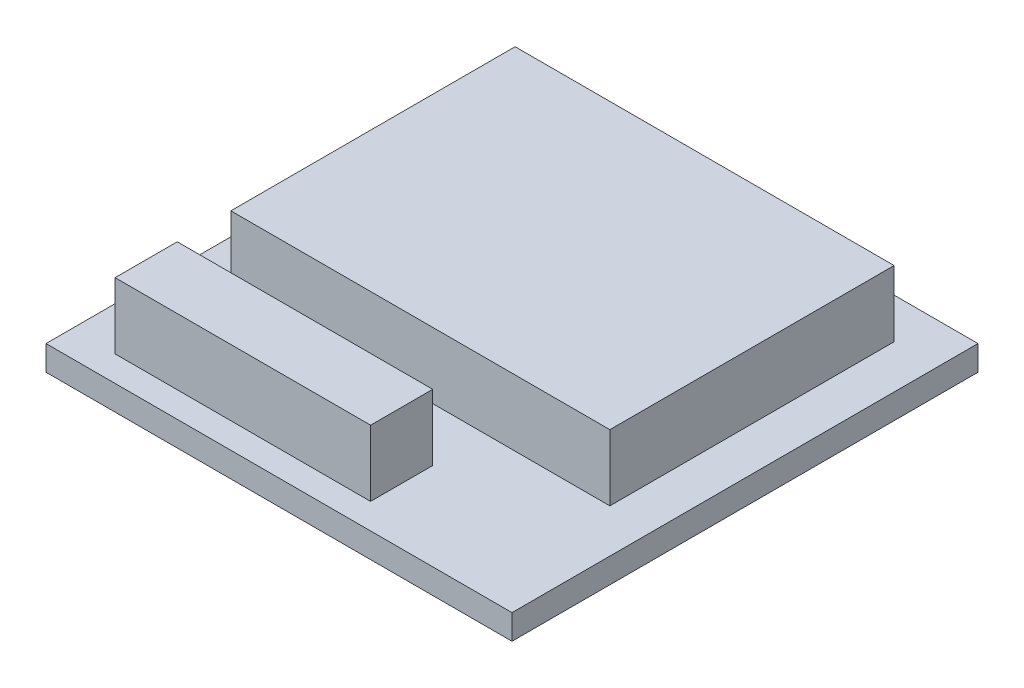
SolidWorks part; units mm, degrees
ref_plane "Front Plane" through (0, 0, 0) normal (0, 0, 1) x (1, 0, 0)
ref_plane "Top Plane" through (0, 0, 0) normal (0, 1, 0) x (1, 0, 0)
ref_plane "Right Plane" through (0, 0, 0) normal (1, 0, 0) x (0, 0, -1)
sketch "Sketch1" plane through (0, 0, 0) normal (0, 1, 0) x (1, 0, 0)
  line L1 (-7.62, -7.62) -> (7.62, -7.62)
  line L2 (-7.62, -7.62) -> (-7.62, 7.62)
  line L3 (-7.62, 7.62) -> (7.62, 7.62)
  line L4 (7.62, -7.62) -> (7.62, 7.62)
  line L5 (-7.62, -7.62) -> (7.62, 7.62) construction
  line L6 (-7.62, 7.62) -> (7.62, -7.62) construction
  point P0 (0, 0)
extrude "Boss-Extrude1" add sketch "Sketch1" along normal blind 0.8128
sketch "Sketch2" plane through (0, 0.8128, 0) normal (0, 1, 0) x (-1, 0, 0)
  line L0 (7.62, -7.62) -> (6.1976, -7.62) construction
  line L1 (-7.62, -7.62) -> (7.62, -7.62) construction
  line L2 (6.1976, -7.62) -> (6.1976, -6.2992) construction
  line L3 (7.62, 7.62) -> (7.62, 6.7829) construction
  line L4 (6.1976, -6.2992) -> (-6.1976, -6.2992)
  line L5 (6.1976, -6.2992) -> (6.1976, 2.9972)
  line L6 (6.1976, 2.9972) -> (-6.1976, 2.9972)
  line L7 (-6.1976, -6.2992) -> (-6.1976, 2.9972)
  line L8 (7.62, -7.62) -> (7.62, 7.62) construction
  line L9 (7.62, 6.7829) -> (6.1976, 6.7829) construction
  line L11 (6.1976, 6.7829) -> (-2.1584, 6.7829)
  line L12 (6.1976, 6.7829) -> (6.1976, 4.7509)
  line L13 (6.1976, 4.7509) -> (-2.1584, 4.7509)
  line L14 (-2.1584, 6.7829) -> (-2.1584, 4.7509)
extrude "Boss-Extrude2" add sketch "Sketch2" along normal blind 2.159 separate body
